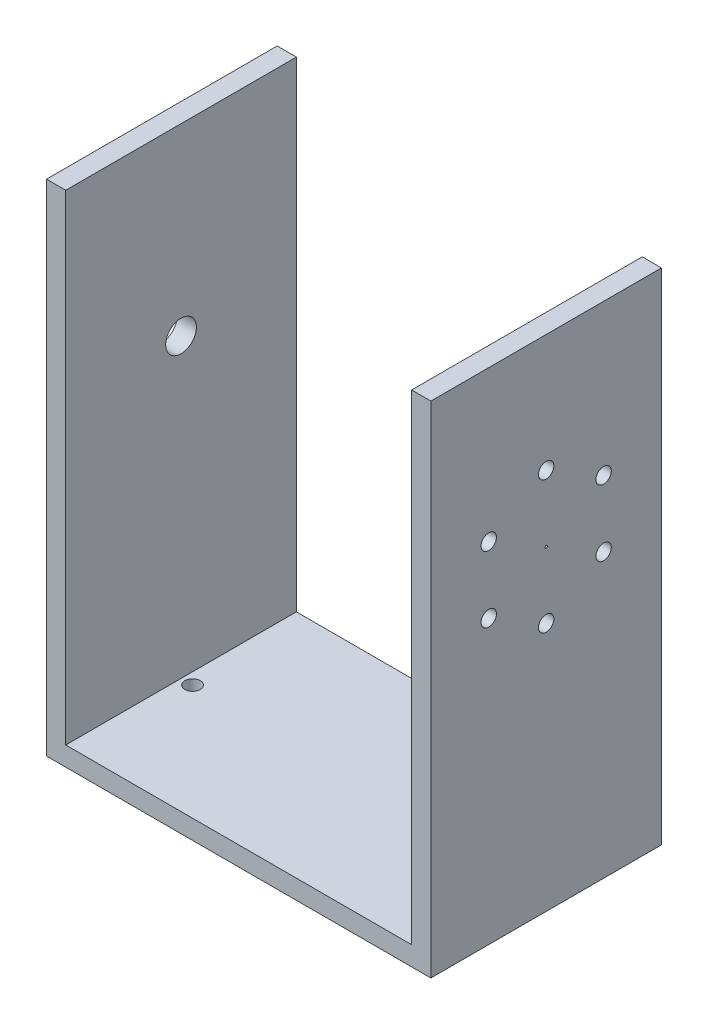
SolidWorks part; units mm, degrees
ref_plane "前视基准面" through (0, 0, 0) normal (0, 0, 1) x (1, 0, 0)
ref_plane "上视基准面" through (0, 0, 0) normal (0, 1, 0) x (1, 0, 0)
ref_plane "右视基准面" through (0, 0, 0) normal (1, 0, 0) x (0, 0, -1)
other "Configuration Table"
sketch "草图1" plane through (0, 0, 0) normal (0, 0, 1) x (1, 0, 0)
  line L1 (95, -81.8373) -> (95, 48.1627)
  line L2 (95, 48.1627) -> (90, 48.1627)
  line L3 (90, 48.1627) -> (90, -76.8373)
  line L4 (90, -76.8373) -> (0, -76.8373)
  line L5 (0, -76.8373) -> (0, 48.1627)
  line L6 (0, 48.1627) -> (-5, 48.1627)
  line L7 (-5, 48.1627) -> (-5, -81.8373)
  line L9 (-5, -81.8373) -> (95, -81.8373)
  dimension "D1" = 100
  dimension "D2" = 90
  dimension "D3" = 5
  dimension "D4" = 130
  dimension "D5" = 5
  dimension "D6" = 130
extrude "凸台-拉伸1" add sketch "草图1" along normal blind 60
sketch "草图2" plane through (0, -76.8373, 0) normal (0, 1, 0) x (1, 0, 0)
  line L0 (0, -30) -> (89.4788, -30) construction
  line L2 (-5, -60) -> (-5, 0) construction
  line L3 (95, -60) -> (95, 0) construction
  circle A0 centre (3, -30) radius 2
  circle A1 centre (87, -30) radius 2
  dimension "D1" = 8
  dimension "D2" = 8
extrude "切除-拉伸1" cut sketch "草图2" against normal through all
sketch "草图3" plane through (90, 0, 0) normal (-1, 0, 0) x (0, 0, 1)
  line L0 (0, 0) -> (60, 0.6627) construction
  line L3 (30, 48.1627) -> (30, 0.3314) construction
  circle A0 centre (30, 17.5824) radius 2
  circle A1 centre (15.0602, 8.9569) radius 2
  circle A2 centre (15.0602, -8.2942) radius 2
  circle A3 centre (30, -16.9197) radius 2
  circle A4 centre (44.9398, -8.2942) radius 2
  circle A5 centre (44.9398, 8.9569) radius 2
  circle A6 centre (30, 0.3314) radius 0.3238
  point P2 (30, 0.3314)
  point P19 (30, 0.3314)
  dimension "D1" = 17.25
  dimension "D2" = 6
extrude "切除-拉伸2" cut sketch "草图3" against normal blind 10
sketch "草图5" plane through (0, 0, 0) normal (1, 0, 0) x (0, 0, -1)
  line L4 (0, -76.8373) -> (0, 48.1627)
  line L5 (0, 48.1627) -> (-60, 48.1627)
  line L6 (-60, 48.1627) -> (-60, -76.8373)
  line L7 (-60, -76.8373) -> (0, -76.8373)
  line L8 (0, -76.8373) -> (0, 48.1627)
  line L9 (0, 48.1627) -> (-60, 48.1627)
  line L10 (-60, 48.1627) -> (-60, -76.8373)
  line L11 (-60, -76.8373) -> (0, -76.8373)
  circle A0 centre (-30, 0.3314) radius 0.3238 construction
  circle A1 centre (-30, 0.3314) radius 0.3238
  circle A2 centre (-30, 0.3314) radius 4
  point P7 (0, 0)
  point P9 (0, 0)
  dimension "D1" = 0
extrude "切除-拉伸4" cut sketch "草图5" against normal through all contours A2 A1 | A1
